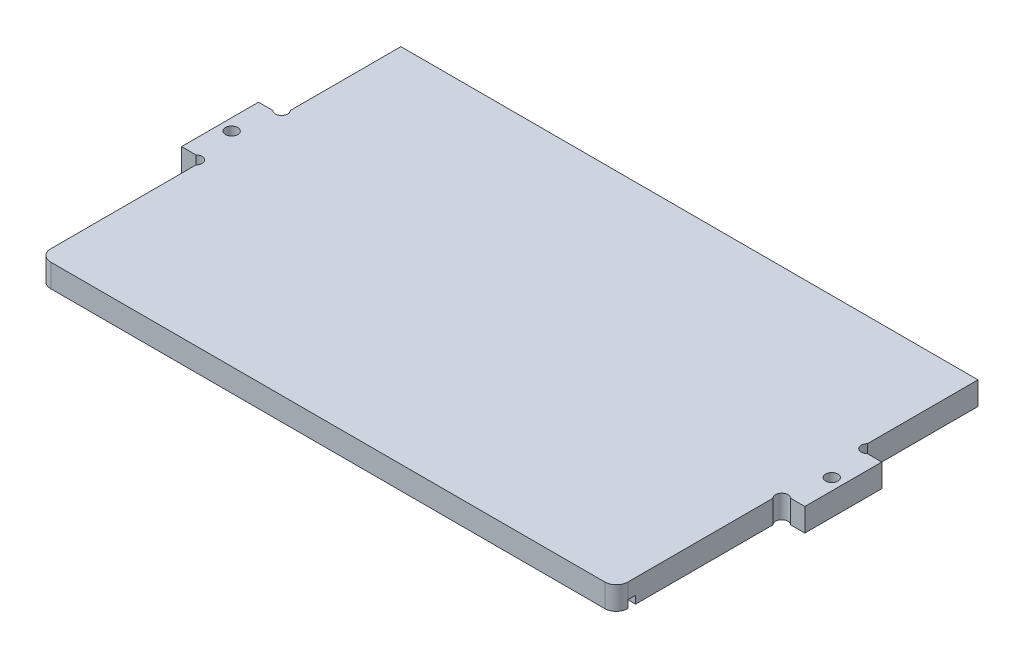
SolidWorks part; units mm, degrees
ref_plane "Plan de face" through (0, 0, 0) normal (0, 0, 1) x (1, 0, 0)
ref_plane "Plan de dessus" through (0, 0, 0) normal (0, 1, 0) x (1, 0, 0)
ref_plane "Plan de droite" through (0, 0, 0) normal (1, 0, 0) x (0, 0, -1)
sketch "Esquisse1" plane through (0, 0, 0) normal (0, 1, 0) x (1, 0, 0)
  line L0 (-8.6273, 0) -> (192.2035, 0) construction
  line L1 (-8.6273, 6) -> (173.7994, 6) construction
  line L2 (6, 98.6212) -> (6, -11.0942) construction
  line L3 (173.7994, 44) -> (-8.6273, 44) construction
  line L4 (42.3876, 34) -> (-8.6273, 34) construction
  line L5 (0, -11.0942) -> (0, 122.8371) construction
  line L6 (81, 29.7469) -> (81, 110.8906) construction
  line L7 (-8.6273, 82) -> (192.2035, 82) construction
  line L8 (3, 40.6824) -> (3, 66.3443) construction
  line L9 (6, 34) -> (-13.4408, 14.5592) construction
  line L10 (16.014, 20) -> (42.3876, 20) construction
  line L11 (162, 122.8371) -> (162, -17.5193) construction
  line L12 (6, 56.2627) -> (6, 85)
  line L13 (3.7373, 54) -> (0, 54)
  line L14 (0, 54) -> (0, 34)
  line L15 (0, 34) -> (3.7373, 34)
  line L16 (6, 31.7373) -> (6, -6)
  line L17 (9, -9) -> (153, -9)
  line L18 (156, -6) -> (156, 31.7373)
  line L19 (-8.6273, 85) -> (167.6047, 85) construction
  line L22 (162, 34) -> (158.2627, 34)
  line L23 (162, 54) -> (162, 34)
  line L24 (158.2627, 54) -> (162, 54)
  line L25 (156, 56.2627) -> (156, 85)
  line L26 (6, 85) -> (156, 85)
  line L29 (-8.6273, -9) -> (192.2035, -9) construction
  circle A0 centre (3, 44) radius 1.6
  arc A1 (6, 31.7373) -> (3.7373, 34) centre (4.8686, 32.8686) ccw
  arc A2 (153, -9) -> (156, -6) centre (153, -6) ccw
  arc A3 (6, 56.2627) -> (3.7373, 54) centre (4.8686, 55.1314) cw
  arc A4 (156, 56.2627) -> (158.2627, 54) centre (157.1314, 55.1314) ccw
  arc A5 (6, -6) -> (9, -9) centre (9, -6) ccw
  arc A6 (156, 31.7373) -> (158.2627, 34) centre (157.1314, 32.8686) cw
  circle A7 centre (159, 44) radius 1.6
  point P41 (156, -9)
  point P46 (6, -9)
  point P63 (162, 0)
  point P66 (0, 0)
  dimension "D10" = 14
  dimension "D12" = 3
  dimension "D1" = 162
  dimension "D2" = 82
  dimension "D3" = 6
  dimension "D4" = 38
  dimension "D5" = 10
  dimension "D6" = 6
  dimension "D7" = 81
  dimension "D8" = 3
  dimension "D9" = 45
  dimension "D11" = 3
  dimension "D13" = 9
extrude "Boss.-Extru.1" add sketch "Esquisse1" along normal blind 6
sketch "Esquisse2" plane through (0, 0, 0) normal (0, -1, 0) x (1, 0, 0)
  line L0 (160.46, 9) -> (-12.445, 9) construction
  line L1 (-12.445, 6) -> (160.46, 6) construction
  line L2 (-12.445, 4) -> (160.46, 4) construction
  line L3 (156, 19.6085) -> (156, -7.0901) construction
  line L4 (156, 6) -> (156, -31.7373) construction
  line L5 (6, 19.6085) -> (6, -4.0706) construction
  line L6 (6, -31.7373) -> (6, 6) construction
  line L8 (6, 6) -> (156, 6)
  line L9 (6, 6) -> (6, 4)
  line L10 (6, 4) -> (156, 4)
  line L11 (156, 6) -> (156, 4)
  dimension "D1" = 3
  dimension "D2" = 2
extrude "Enlèv. mat.-Extru.1" cut sketch "Esquisse2" against normal blind 2
